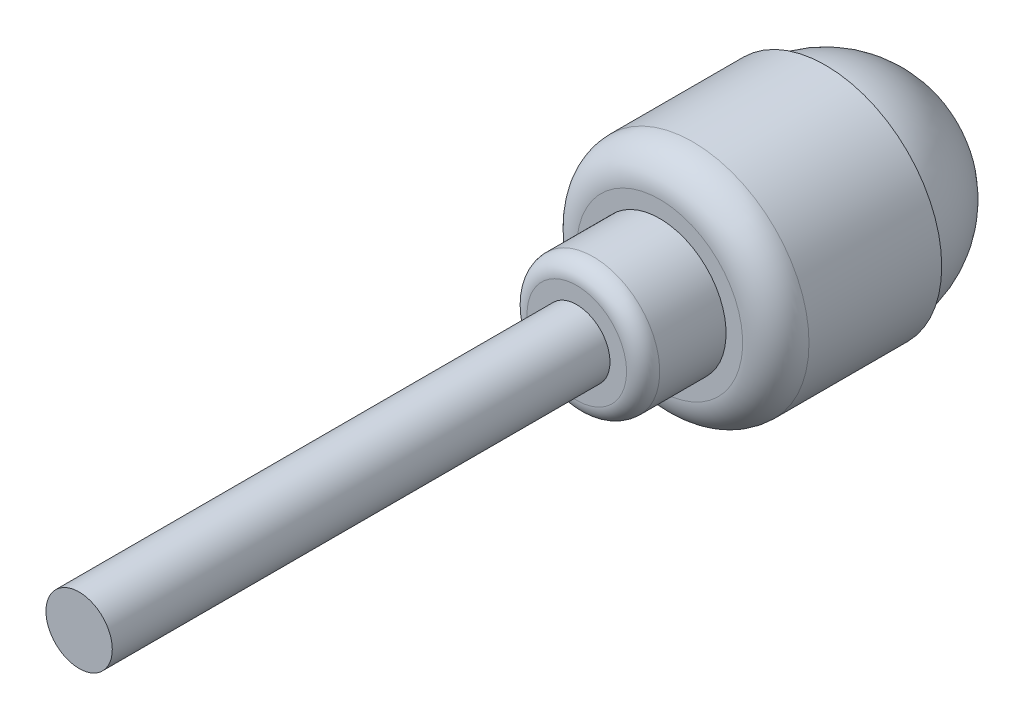
SolidWorks part; units mm, degrees
ref_plane "Front Plane" through (0, 0, 0) normal (0, 0, 1) x (1, 0, 0)
ref_plane "Top Plane" through (0, 0, 0) normal (0, 1, 0) x (1, 0, 0)
ref_plane "Right Plane" through (0, 0, 0) normal (1, 0, 0) x (0, 0, -1)
sketch "Sketch1" plane through (0, 0, 0) normal (0, 1, 0) x (1, 0, 0)
  line L0 (0, 0) -> (4, 0)
  line L1 (4, 0) -> (4, 5)
  line L2 (4, 5) -> (7, 5)
  line L3 (7, 5) -> (7, 15)
  line L4 (7, 15) -> (6.5, 15)
  line L5 (0, 21.5) -> (0, 0)
  line L6 (0, 21.5) -> (-2.3183, 21.5) construction
  line L7 (6.5, 15) -> (6.5, 13.8515) construction
  arc A0 (6.5, 15) -> (0, 21.5) centre (0, 15) ccw
  dimension "D1" = 4
  dimension "D2" = 3
  dimension "D3" = 0.5
  dimension "D4" = 5
  dimension "D5" = 10
revolve "Revolve1" add sketch "Sketch1" angle 360 about L5
sketch "Sketch2" plane through (0, 0, 0) normal (0, 0, 1) x (1, 0, 0)
  circle A0 centre (0, 0) radius 2
  dimension "D1" = 4
extrude "Boss-Extrude1" add sketch "Sketch2" along normal blind 30
fillet "Fillet1" radius 2 1 edges at (-7, 0, -5)
fillet "Fillet2" radius 1 1 edges at (-4, 0, 0)
